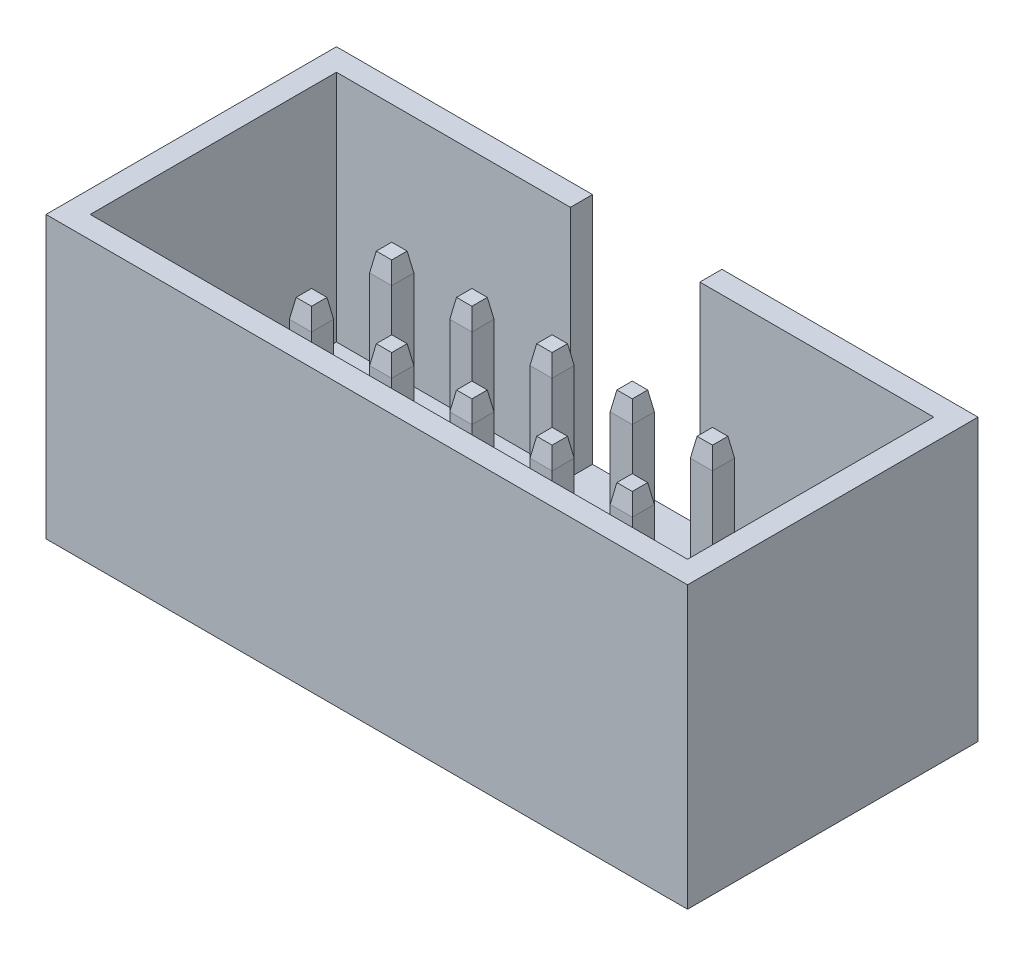
SolidWorks part; units mm, degrees
ref_plane "Płaszczyzna przednia" through (0, 0, 0) normal (0, 0, 1) x (1, 0, 0)
ref_plane "Płaszczyzna górna" through (0, 0, 0) normal (0, 1, 0) x (1, 0, 0)
ref_plane "Płaszczyzna prawa" through (0, 0, 0) normal (1, 0, 0) x (0, 0, -1)
sketch "Szkic1" plane through (0, 0, 0) normal (0, 1, 0) x (1, 0, 0)
  line L1 (0, 9.2) -> (20.32, 9.2)
  line L2 (0, 9.2) -> (0, 0)
  line L3 (0, 0) -> (20.32, 0)
  line L4 (20.32, 9.2) -> (20.32, 0)
  dimension "D1" = 20.32
  dimension "D2" = 9.2
extrude "Dodanie-wyciągnięcie1" add sketch "Szkic1" along normal blind 8.9
sketch "Szkic2" plane through (0, 8.9, 0) normal (0, 1, 0) x (1, 0, 0)
  line L0 (0, 9.2) -> (0, 0) construction
  line L1 (0.7, 8.5) -> (19.62, 8.5)
  line L2 (0.7, 8.5) -> (0.7, 0.7)
  line L3 (0.7, 0.7) -> (19.62, 0.7)
  line L4 (19.62, 8.5) -> (19.62, 0.7)
  line L5 (20.32, 0) -> (20.32, 9.2) construction
  line L6 (20.32, 9.2) -> (0, 9.2) construction
  line L7 (0, 0) -> (20.32, 0) construction
  dimension "D1" = 0.7
  dimension "D2" = 0.7
  dimension "D3" = 0.7
  dimension "D4" = 0.7
extrude "Wytnij-wyciągnięcie1" cut sketch "Szkic2" against normal blind 7.4
sketch "Szkic3" plane through (0, 8.9, 0) normal (0, 1, 0) x (1, 0, 0)
  line L0 (8.11, 9.2) -> (8.11, 8.5)
  line L1 (20.32, 9.2) -> (0, 9.2) construction
  line L2 (19.62, 8.5) -> (0.7, 8.5) construction
  line L3 (8.11, 8.5) -> (12.21, 8.5)
  line L4 (19.62, 8.5) -> (0.7, 8.5) construction
  line L5 (12.21, 8.5) -> (12.21, 9.2)
  line L6 (12.21, 9.2) -> (8.11, 9.2)
  line L7 (0, 9.2) -> (0, 0) construction
  dimension "D1" = 4.1
  dimension "D2" = 8.11
extrude "Wytnij-wyciągnięcie2" cut sketch "Szkic3" against normal blind 7.4
sketch "Szkic4" plane through (0, 1.5, 0) normal (0, 1, 0) x (1, 0, 0)
  line L0 (8.11, 8.5) -> (0.7, 8.5) construction
  line L1 (4.73, 6.22) -> (5.43, 6.22)
  line L2 (4.73, 6.22) -> (4.73, 5.52)
  line L3 (4.73, 5.52) -> (5.43, 5.52)
  line L4 (5.43, 6.22) -> (5.43, 5.52)
  line L5 (4.73, 6.22) -> (5.43, 5.52) construction
  line L6 (4.73, 5.52) -> (5.43, 6.22) construction
  line L7 (0.7, 8.5) -> (0.7, 0.7) construction
  line L8 (7.27, 6.22) -> (7.97, 6.22)
  line L9 (7.27, 6.22) -> (7.27, 5.52)
  line L10 (7.97, 6.22) -> (7.97, 5.52)
  line L11 (7.27, 5.52) -> (7.97, 5.52)
  line L12 (9.81, 6.22) -> (10.51, 6.22)
  line L13 (9.81, 6.22) -> (9.81, 5.52)
  line L14 (10.51, 6.22) -> (10.51, 5.52)
  line L15 (9.81, 5.52) -> (10.51, 5.52)
  line L16 (12.35, 6.22) -> (13.05, 6.22)
  line L17 (12.35, 6.22) -> (12.35, 5.52)
  line L18 (13.05, 6.22) -> (13.05, 5.52)
  line L19 (12.35, 5.52) -> (13.05, 5.52)
  line L20 (14.89, 6.22) -> (15.59, 6.22)
  line L21 (14.89, 6.22) -> (14.89, 5.52)
  line L22 (15.59, 6.22) -> (15.59, 5.52)
  line L23 (14.89, 5.52) -> (15.59, 5.52)
  line L24 (7.27, 3.68) -> (7.97, 3.68)
  line L25 (7.27, 3.68) -> (7.27, 2.98)
  line L26 (7.97, 3.68) -> (7.97, 2.98)
  line L27 (7.27, 2.98) -> (7.97, 2.98)
  line L28 (9.81, 3.68) -> (10.51, 3.68)
  line L29 (9.81, 3.68) -> (9.81, 2.98)
  line L30 (10.51, 3.68) -> (10.51, 2.98)
  line L31 (9.81, 2.98) -> (10.51, 2.98)
  line L32 (12.35, 3.68) -> (13.05, 3.68)
  line L33 (12.35, 3.68) -> (12.35, 2.98)
  line L34 (13.05, 3.68) -> (13.05, 2.98)
  line L35 (12.35, 2.98) -> (13.05, 2.98)
  line L36 (14.89, 3.68) -> (15.59, 3.68)
  line L37 (14.89, 3.68) -> (14.89, 2.98)
  line L38 (15.59, 3.68) -> (15.59, 2.98)
  line L39 (14.89, 2.98) -> (15.59, 2.98)
  line L40 (4.73, 3.68) -> (5.43, 3.68)
  line L41 (4.73, 3.68) -> (4.73, 2.98)
  line L42 (5.43, 3.68) -> (5.43, 2.98)
  line L43 (4.73, 2.98) -> (5.43, 2.98)
  point P0 (5.08, 5.87)
  dimension "D1" = 0.7
  dimension "D2" = 2.63
  dimension "D3" = 4.38
  dimension "D4" = 5
  dimension "D5" = 2
extrude "Dodanie-wyciągnięcie2" add sketch "Szkic4" along normal blind 6 and the other way blind 4
chamfer "Sfazowanie1" distance 0.6 angle 10 40 edges at (5.08, 7.5, -6.22) (5.43, 7.5, -5.87) (4.73, 7.5, -5.87) (5.08, 7.5, -5.52) (14.89, 7.5, -3.33) (15.24, 7.5, -3.68) (15.59, 7.5, -3.33) (15.24, 7.5, -2.98) (14.89, 7.5, -5.87) (15.24, 7.5, -6.22) (15.59, 7.5, -5.87) (15.24, 7.5, -5.52) (12.35, 7.5, -5.87) (12.7, 7.5, -6.22) (13.05, 7.5, -5.87) (12.7, 7.5, -5.52) (12.35, 7.5, -3.33) (12.7, 7.5, -3.68) (13.05, 7.5, -3.33) (12.7, 7.5, -2.98) (9.81, 7.5, -5.87) (10.16, 7.5, -6.22) (10.51, 7.5, -5.87) (10.16, 7.5, -5.52) (9.81, 7.5, -3.33) (10.16, 7.5, -3.68) (10.51, 7.5, -3.33) (10.16, 7.5, -2.98) (7.62, 7.5, -2.98) (7.97, 7.5, -3.33) (7.62, 7.5, -3.68) (7.27, 7.5, -3.33) (5.43, 7.5, -3.33) (5.08, 7.5, -2.98) (4.73, 7.5, -3.33) (5.08, 7.5, -3.68) (7.62, 7.5, -6.22) (7.97, 7.5, -5.87) (7.62, 7.5, -5.52) (7.27, 7.5, -5.87)
chamfer "Sfazowanie2" distance 0.6 angle 10 40 edges at (5.43, -2.5, -3.33) (5.08, -2.5, -2.98) (5.08, -2.5, -3.68) (4.73, -2.5, -3.33) (15.59, -2.5, -5.87) (15.24, -2.5, -6.22) (14.89, -2.5, -5.87) (15.24, -2.5, -5.52) (15.59, -2.5, -3.33) (15.24, -2.5, -3.68) (14.89, -2.5, -3.33) (15.24, -2.5, -2.98) (13.05, -2.5, -3.33) (12.7, -2.5, -3.68) (12.35, -2.5, -3.33) (12.7, -2.5, -2.98) (13.05, -2.5, -5.87) (12.7, -2.5, -6.22) (12.35, -2.5, -5.87) (12.7, -2.5, -5.52) (10.51, -2.5, -5.87) (10.16, -2.5, -6.22) (9.81, -2.5, -5.87) (10.16, -2.5, -5.52) (10.51, -2.5, -3.33) (10.16, -2.5, -3.68) (9.81, -2.5, -3.33) (10.16, -2.5, -2.98) (7.97, -2.5, -3.33) (7.62, -2.5, -3.68) (7.27, -2.5, -3.33) (7.62, -2.5, -2.98) (7.97, -2.5, -5.87) (7.62, -2.5, -6.22) (7.27, -2.5, -5.87) (7.62, -2.5, -5.52) (5.08, -2.5, -6.22) (4.73, -2.5, -5.87) (5.08, -2.5, -5.52) (5.43, -2.5, -5.87)
